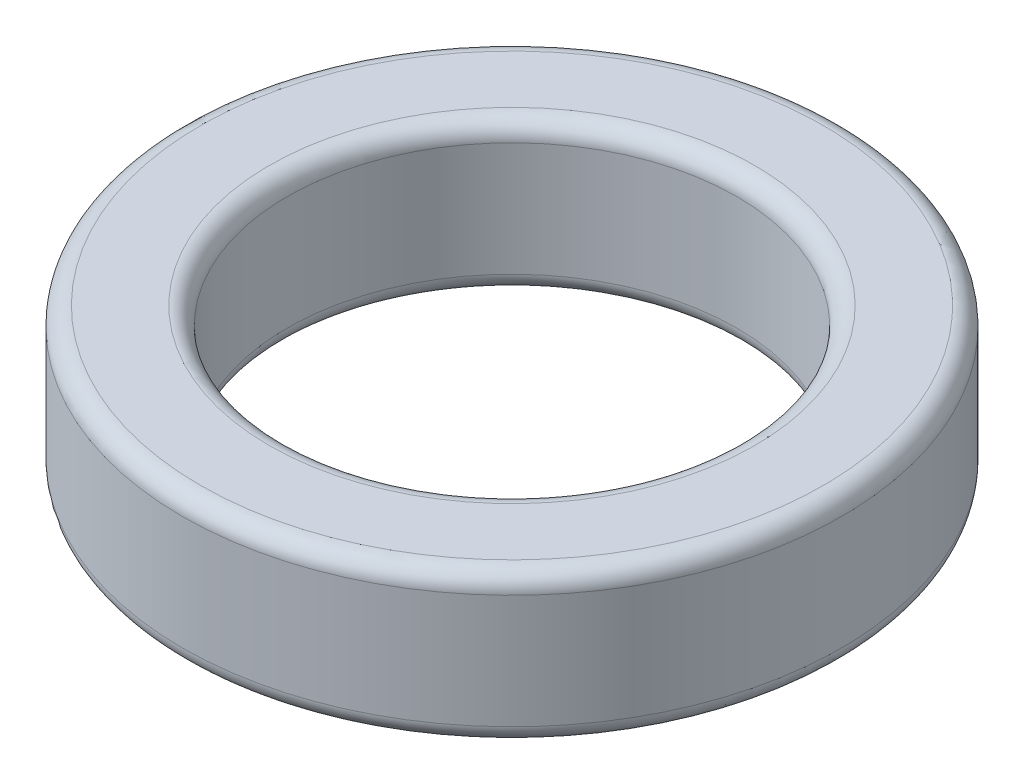
SolidWorks part; units mm, degrees
ref_plane "Спереди" through (0, 0, 0) normal (0, 0, 1) x (1, 0, 0)
ref_plane "Сверху" through (0, 0, 0) normal (0, 1, 0) x (1, 0, 0)
ref_plane "Справа" through (0, 0, 0) normal (1, 0, 0) x (0, 0, -1)
sketch "Эскиз1" plane through (0, 0, 0) normal (0, 0, 1) x (1, 0, 0)
  line L0 (3.75, 0) -> (3.75, 2.5)
  line L1 (3.75, 2.5) -> (5.5, 2.5)
  line L2 (5.5, 2.5) -> (5.5, 0)
  line L5 (5.5, 0) -> (3.75, 0)
  line L6 (0, 0) -> (0, 17.7782) construction
  dimension "D2" = 7.5
  dimension "D3" = 11
  dimension "D5" = 2.5
revolve "Повернуть1" add sketch "Эскиз1" angle 360 about L6
fillet "Скругление1" radius 0.3 4 edges at (0, 2.5, -5.5) (0, 0, -5.5) (0, 0, -3.75) (0, 2.5, -3.75)
